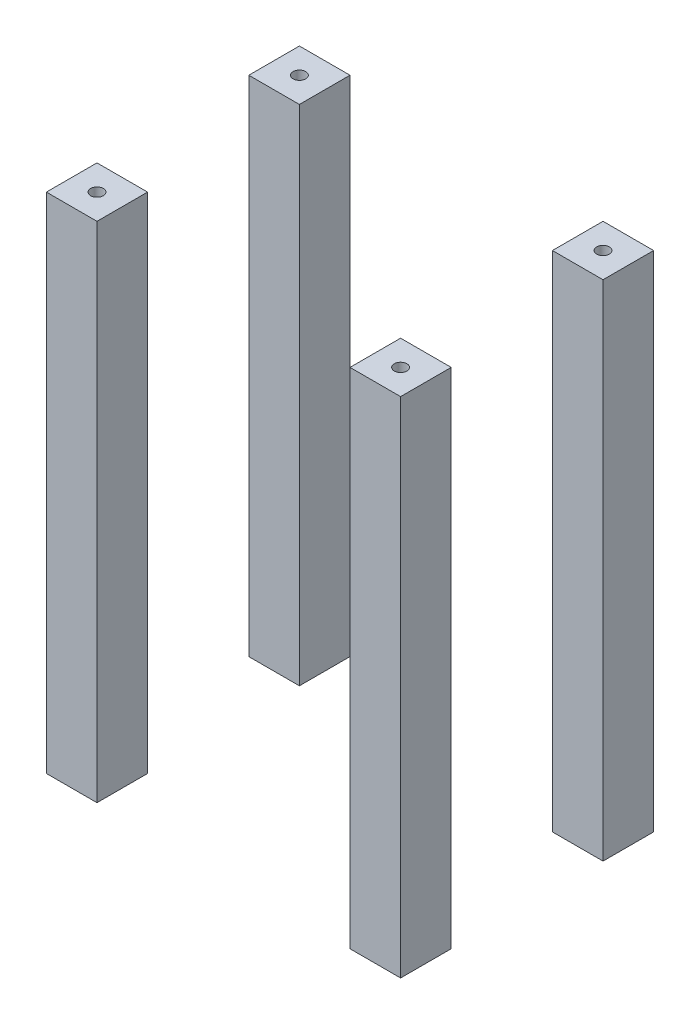
SolidWorks part; units mm, degrees
ref_plane "Ebene vorne" through (0, 0, 0) normal (0, 0, 1) x (1, 0, 0)
ref_plane "Ebene oben" through (0, 0, 0) normal (0, 1, 0) x (1, 0, 0)
ref_plane "Ebene rechts" through (0, 0, 0) normal (1, 0, 0) x (0, 0, -1)
sketch "Top" plane through (0, 0, 0) normal (0, 1, 0) x (1, 0, 0)
  line L1 (-70, -132.65) -> (70, -132.65)
  line L2 (-70, -132.65) -> (-70, -32.65)
  line L3 (-70, -32.65) -> (70, -32.65)
  line L4 (70, -132.65) -> (70, -32.65)
  line L5 (-70, -132.65) -> (70, -32.65) construction
  line L6 (-70, -32.65) -> (70, -132.65) construction
  line L8 (-70, -132.65) -> (-50, -132.65)
  line L9 (-70, -132.65) -> (-70, -112.65)
  line L10 (-70, -112.65) -> (-50, -112.65)
  line L11 (-50, -132.65) -> (-50, -112.65)
  line L12 (50, -132.65) -> (50, -112.65)
  line L13 (70, -112.65) -> (50, -112.65)
  line L14 (70, -132.65) -> (70, -112.65)
  line L15 (70, -132.65) -> (50, -132.65)
  line L16 (0, -82.65) -> (44.0576, -82.65) construction
  line L17 (70, -32.65) -> (50, -32.65)
  line L18 (70, -32.65) -> (70, -52.65)
  line L19 (70, -52.65) -> (50, -52.65)
  line L20 (50, -32.65) -> (50, -52.65)
  line L21 (-50, -32.65) -> (-50, -52.65)
  line L22 (-70, -52.65) -> (-50, -52.65)
  line L23 (-70, -32.65) -> (-70, -52.65)
  line L24 (-70, -32.65) -> (-50, -32.65)
  circle A0 centre (-60, -122.65) radius 3
  circle A1 centre (60, -122.65) radius 3
  circle A2 centre (60, -42.65) radius 3
  circle A3 centre (-60, -42.65) radius 3
  point P0 (0, -82.65)
sketch "BaseplateHeight" plane through (0, 0, 0) normal (1, 0, 0) x (0, 0, -1)
  line L1 (-32.65, 205) -> (-132.65, 205)
  line L2 (-32.65, 205) -> (-32.65, 199)
  line L3 (-32.65, 199) -> (-132.65, 199)
  line L4 (-132.65, 205) -> (-132.65, 199)
sketch "Skizze3" plane through (0, 0, 0) normal (0, 1, 0) x (1, 0, 0)
  line L1 (-70, -32.65) -> (-50, -32.65)
  line L2 (-70, -32.65) -> (-70, -52.65)
  line L3 (-70, -52.65) -> (-50, -52.65)
  line L4 (-50, -32.65) -> (-50, -52.65)
  line L5 (50, -32.65) -> (70, -32.65)
  line L6 (50, -32.65) -> (50, -52.65)
  line L7 (50, -52.65) -> (70, -52.65)
  line L8 (70, -32.65) -> (70, -52.65)
  line L9 (50, -112.65) -> (70, -112.65)
  line L10 (50, -112.65) -> (50, -132.65)
  line L11 (50, -132.65) -> (70, -132.65)
  line L12 (70, -112.65) -> (70, -132.65)
  line L13 (-70, -112.65) -> (-50, -112.65)
  line L14 (-70, -112.65) -> (-70, -132.65)
  line L15 (-70, -132.65) -> (-50, -132.65)
  line L16 (-50, -112.65) -> (-50, -132.65)
  circle A0 centre (-60, -42.65) radius 2.5
  circle A1 centre (-60, -122.65) radius 2.5
  circle A2 centre (60, -42.65) radius 2.5
  circle A3 centre (60, -122.65) radius 2.5
extrude "Aufsatz-Linear austragen1" add sketch "Skizze3" along normal up to vertex (199 mm away) up to point (0, 199, 132.65)
